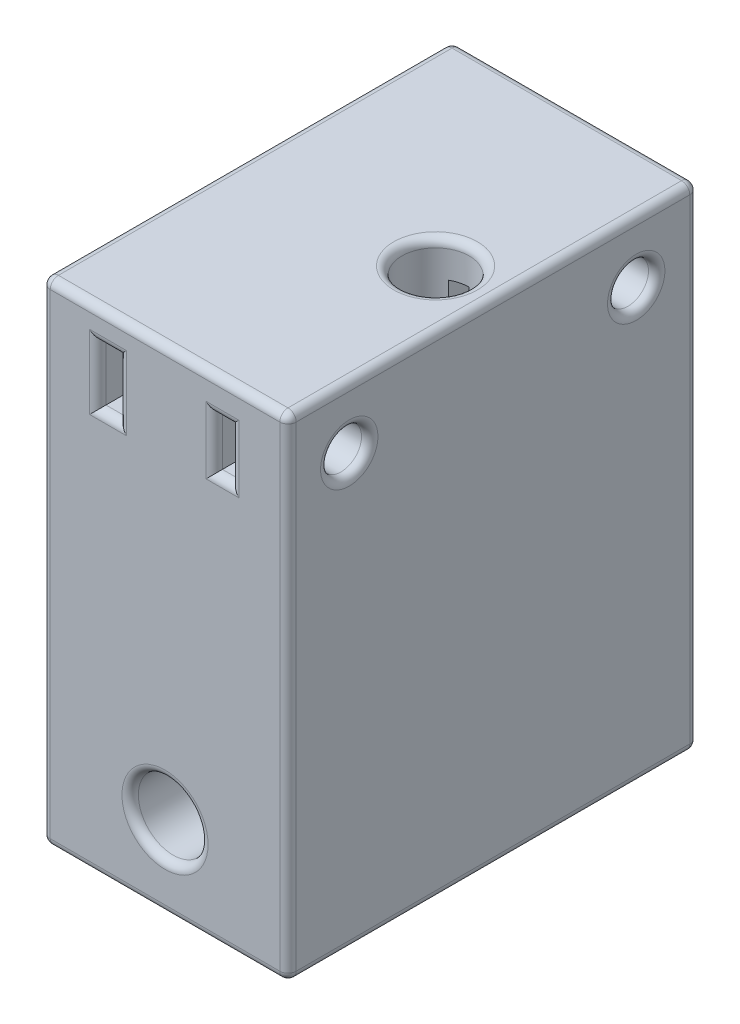
SolidWorks part; units mm, degrees
ref_plane "前视基准面" through (0, 0, 0) normal (0, 0, 1) x (1, 0, 0)
ref_plane "上视基准面" through (0, 0, 0) normal (0, 1, 0) x (1, 0, 0)
ref_plane "右视基准面" through (0, 0, 0) normal (1, 0, 0) x (0, 0, -1)
sketch "草图1" plane through (0, 0, 0) normal (0, 0, 1) x (1, 0, 0)
  line L1 (-8.6305, 51.447) -> (21.3695, 51.447)
  line L2 (-8.6305, 51.447) -> (-8.6305, -8.553)
  line L3 (-8.6305, -8.553) -> (21.3695, -8.553)
  line L4 (21.3695, 51.447) -> (21.3695, -8.553)
  circle A0 centre (6.3695, 1.447) radius 4.25
  dimension "D3" = 8.5
  dimension "D1" = 30
  dimension "D2" = 60
  dimension "D4" = 10
extrude "凸台-拉伸1" add sketch "草图1" along normal blind 50
sketch "草图2" plane through (0, 0, 50) normal (0, 0, 1) x (1, 0, 0)
  line L0 (21.3695, -8.553) -> (21.3695, 51.447) construction
  line L1 (-1.8305, 47.647) -> (0.6695, 47.647)
  line L2 (-1.8305, 47.647) -> (-1.8305, 40.647)
  line L3 (-1.8305, 40.647) -> (0.6695, 40.647)
  line L4 (0.6695, 47.647) -> (0.6695, 40.647)
  line L5 (12.3695, 47.147) -> (14.3695, 47.147)
  line L6 (12.3695, 47.147) -> (12.3695, 40.947)
  line L7 (12.3695, 40.947) -> (14.3695, 40.947)
  line L8 (14.3695, 47.147) -> (14.3695, 40.947)
  line L9 (-8.6305, 51.447) -> (-8.6305, -8.553) construction
  line L10 (21.3695, 51.447) -> (-8.6305, 51.447) construction
  dimension "D1" = 7
  dimension "D2" = 6.8
  dimension "D3" = 2.5
  dimension "D4" = 2
  dimension "D5" = 6.2
  dimension "D6" = 7
  dimension "D7" = 4.3
  dimension "D8" = 3.8
extrude "切除-拉伸1" cut sketch "草图2" against normal blind 50
sketch "草图4" plane through (21.3695, 0, 0) normal (1, 0, 0) x (0, 0, -1)
  line L0 (-50, 51.447) -> (0, 51.447) construction
  circle A0 centre (-42.5325, 43.947) radius 2.5
  circle A1 centre (-7.5325, 43.947) radius 2.5
  dimension "D1" = 5
  dimension "D2" = 7.5
  dimension "D3" = 2
extrude "切除-拉伸2" cut sketch "草图4" against normal blind 7
fillet "圆角1" radius 1 4 edges at (13.3695, 40.947, 50) (12.3695, 44.047, 50) (13.3695, 47.147, 50) (14.3695, 44.047, 50)
fillet "圆角2" radius 1 4 edges at (-0.5805, 40.647, 50) (-1.8305, 44.147, 50) (-0.5805, 47.647, 50) (0.6695, 44.147, 50)
fillet "圆角3" radius 1 1 edges at (10.6195, 1.447, 50)
fillet "圆角4" radius 1 1 edges at (21.3695, 46.447, 42.5325)
fillet "圆角5" radius 1 1 edges at (21.3695, 46.447, 7.5325)
fillet "圆角6" radius 1 9 edges at (-0.5805, 40.647, 0) (0.6695, 44.147, 0) (-1.8305, 44.147, 0) (-0.5805, 47.647, 0) (13.3695, 40.947, 0) (14.3695, 44.047, 0) (13.3695, 47.147, 0) (12.3695, 44.047, 0) (10.6195, 1.447, 0)
sketch "草图5" plane through (0, 51.447, 0) normal (0, 1, 0) x (1, 0, 0)
  line L0 (21.3695, -50) -> (21.3695, 0) construction
  circle A0 centre (14.3695, -25) radius 4.1
  dimension "D1" = 8.2
  dimension "D2" = 7
extrude "切除-拉伸3" cut sketch "草图5" against normal blind 21
fillet "圆角7" radius 1 1 edges at (14.3695, 51.447, 29.1)
fillet "圆角8" radius 1 12 edges at (-8.6305, -8.553, 25) (6.3695, -8.553, 0) (-8.6305, 21.447, 0) (21.3695, 21.447, 0) (21.3695, -8.553, 25) (6.3695, -8.553, 50) (-8.6305, 21.447, 50) (21.3695, 21.447, 50) (6.3695, 51.447, 0) (-8.6305, 51.447, 25) (6.3695, 51.447, 50) (21.3695, 51.447, 25)
